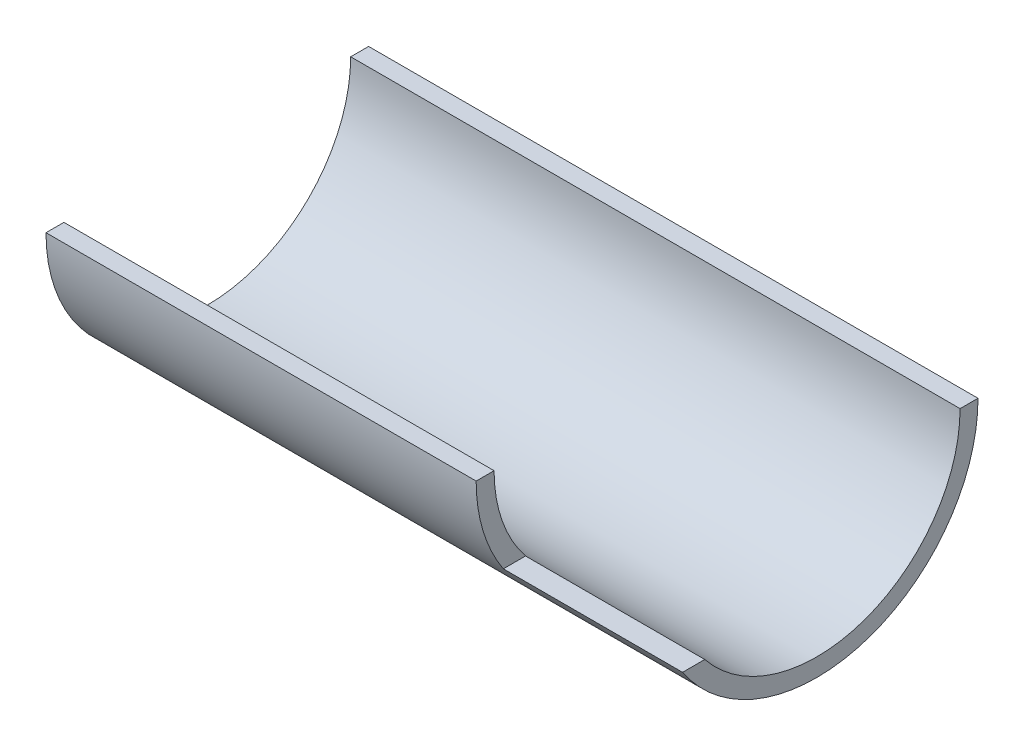
SolidWorks part; units mm, degrees
ref_plane "Front Plane" through (0, 0, 0) normal (0, 0, 1) x (1, 0, 0)
ref_plane "Top Plane" through (0, 0, 0) normal (0, 1, 0) x (1, 0, 0)
ref_plane "Right Plane" through (0, 0, 0) normal (1, 0, 0) x (0, 0, -1)
sketch "Sketch1" plane through (0, 0, 0) normal (1, 0, 0) x (0, 0, -1)
  line L2 (-25.4, 0) -> (-31.75, 0)
  line L3 (31.75, 0) -> (25.4, 0)
  arc A2 (-25.4, 0) -> (25.4, 0) centre (0, 0) ccw
  arc A3 (-31.75, 0) -> (31.75, 0) centre (0, 0) ccw
  dimension "D1" = 31.75
  dimension "D2" = 25.4
  dimension "D3" = 6.35
  dimension "D4" = 6.35
extrude "Boss-Extrude1" add sketch "Sketch1" against normal blind 107.95
sketch "Sketch2" plane through (0, 0, 0) normal (0, 0, 1) x (1, 0, 0)
  line L0 (-107.95, 0) -> (0, 0) construction
  line L1 (-31.75, 0) -> (0, 0)
  line L2 (-31.75, 0) -> (-31.75, -15.875)
  line L3 (-31.75, -15.875) -> (0, -15.875)
  line L4 (0, 0) -> (0, -15.875)
  line L5 (-107.95, 0) -> (-107.95, -31.75) construction
  dimension "D1" = 31.75
  dimension "D2" = 15.875
  dimension "D3" = 76.2
extrude "Cut-Extrude1" cut sketch "Sketch2" along normal blind 127
sketch "Sketch3" plane through (0, 0, 0) normal (1, 0, 0) x (0, 0, -1)
  circle A0 centre (0, 0) radius 28.575
  dimension "D1" = 57.15
extrude "Cut-Extrude2" cut sketch "Sketch3" against normal through all flip side to cut
